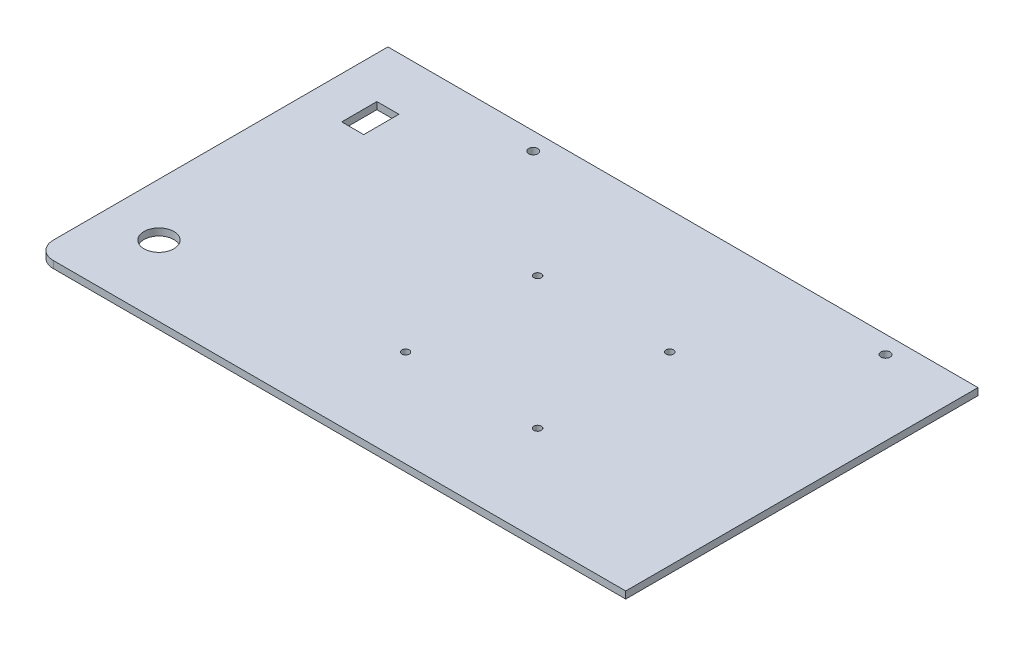
SolidWorks part; units mm, degrees
ref_plane "前视基准面" through (0, 0, 0) normal (0, 0, 1) x (1, 0, 0)
ref_plane "上视基准面" through (0, 0, 0) normal (0, 1, 0) x (1, 0, 0)
ref_plane "右视基准面" through (0, 0, 0) normal (1, 0, 0) x (0, 0, -1)
sketch "草图1" plane through (0, 0, 0) normal (0, 1, 0) x (1, 0, 0)
  line L1 (-142.5, 100) -> (142.5, 100)
  line L2 (-142.5, 100) -> (-142.5, -100)
  line L3 (-142.5, -100) -> (142.5, -100)
  line L4 (142.5, 100) -> (142.5, -100)
  line L5 (-142.5, 100) -> (142.5, -100) construction
  line L6 (-142.5, -100) -> (142.5, 100) construction
  point P0 (0, 0)
  dimension "D1" = 285
  dimension "D2" = 200
extrude "凸台-拉伸1" add sketch "草图1" along normal blind 4
sketch "草图2" plane through (0, 4, 0) normal (0, 1, 0) x (1, 0, 0)
  line L0 (-142.5, 85) -> (142.5, 85) construction
  line L1 (-142.5, 100) -> (-142.5, -100) construction
  line L2 (142.5, -100) -> (142.5, 100) construction
  line L3 (-142.5, -100) -> (142.5, -100) construction
  line L4 (-142.5, 85) -> (142.5, -100) construction
  line L5 (142.5, 85) -> (-142.5, -100) construction
  line L6 (0, -7.5) -> (146.2772, -7.5) construction
  line L7 (0, -7.5) -> (0, 88.4874) construction
  line L8 (142.5, 100) -> (-142.5, 100) construction
  circle A0 centre (-37.5, 30) radius 2.1
  circle A1 centre (37.5, 30) radius 2.1
  circle A2 centre (37.5, -45) radius 2.1
  circle A3 centre (-37.5, -45) radius 2.1
  circle A4 centre (-100, 90) radius 2.6
  circle A5 centre (100, 90) radius 2.6
  dimension "D2" = 4.2
  dimension "D5" = 5.2
  dimension "D1" = 185
  dimension "D3" = 75
  dimension "D4" = 75
  dimension "D6" = 10
  dimension "D7" = 200
extrude "切除-拉伸1" cut sketch "草图2" against normal through all
sketch "草图3" plane through (-142.5, 0, 0) normal (-1, 0, 0) x (0, 0, 1)
  line L1 (-100, 0) -> (100, 0)
  line L2 (-100, 0) -> (-100, 4)
  line L3 (-100, 4) -> (100, 4)
  line L4 (100, 0) -> (100, 4)
extrude "凸台-放按钮的面板" add sketch "草图3" along normal blind 50
sketch "草图4" plane through (0, 0, 0) normal (0, -1, 0) x (1, 0, 0)
  line L0 (142.5, -100) -> (-192.5, -100) construction
  line L1 (-168.75, -50) -> (-156.25, -50)
  line L2 (-168.75, -50) -> (-168.75, -70)
  line L3 (-168.75, -70) -> (-156.25, -70)
  line L4 (-156.25, -50) -> (-156.25, -70)
  line L5 (-168.75, -50) -> (-156.25, -70) construction
  line L6 (-168.75, -70) -> (-156.25, -50) construction
  line L7 (-192.5, -100) -> (-192.5, 100) construction
  line L8 (-192.5, 100) -> (142.5, 100) construction
  circle A0 centre (-162.5, 60) radius 8.5
  point P2 (-162.5, -60)
  dimension "D7" = 17
  dimension "D1" = 12.5
  dimension "D2" = 20
  dimension "D3" = 40
  dimension "D4" = 30
  dimension "D5" = 30
  dimension "D6" = 40
extrude "切除-按钮孔" cut sketch "草图4" against normal through all
fillet "圆角1" radius 10 1 edges at (-192.5, 2, 100)
